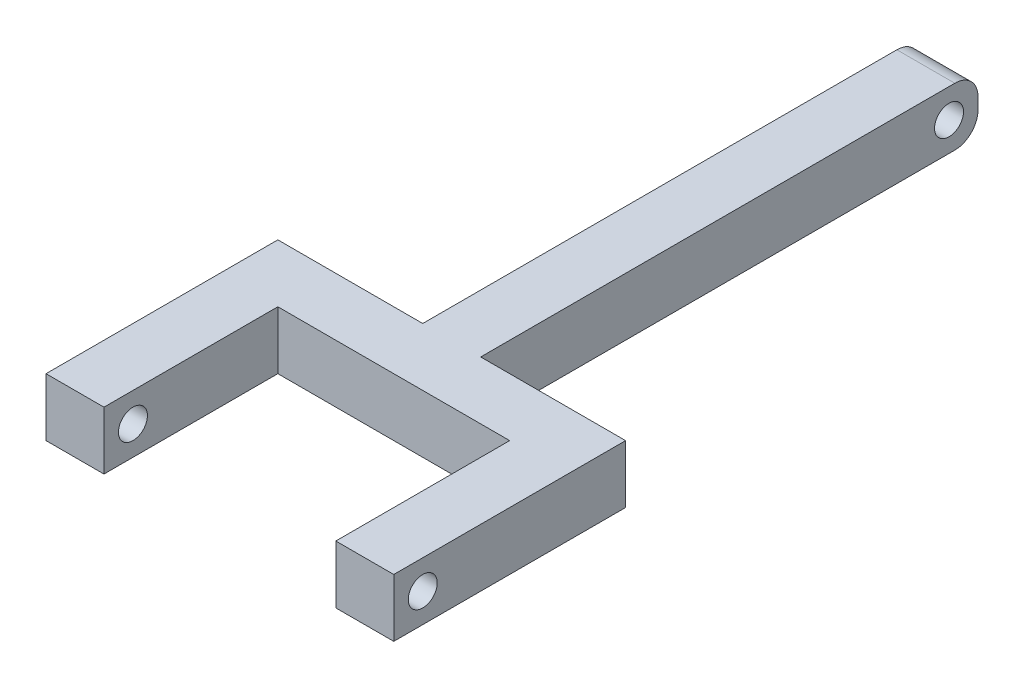
SolidWorks part; units mm, degrees
ref_plane "Front Plane" through (0, 0, 0) normal (0, 0, 1) x (1, 0, 0)
ref_plane "Top Plane" through (0, 0, 0) normal (0, 1, 0) x (1, 0, 0)
ref_plane "Right Plane" through (0, 0, 0) normal (1, 0, 0) x (0, 0, -1)
sketch "Sketch1" plane through (0, 0, 0) normal (0, 0, 1) x (1, 0, 0)
  line L1 (-6.35, -6.35) -> (6.35, -6.35)
  line L2 (-6.35, -6.35) -> (-6.35, 6.35)
  line L3 (-6.35, 6.35) -> (6.35, 6.35)
  line L4 (6.35, -6.35) -> (6.35, 6.35)
  point P4 (0, 6.35)
  point P6 (-6.35, 0)
  dimension "D1" = 12.7
  dimension "D2" = 12.7
  dimension "D3" = 0
  dimension "D4" = 0
extrude "Boss-Extrude1" add sketch "Sketch1" against normal blind 80.01 and the other way blind 41.656
sketch "Sketch4" plane through (0, 0, 0) normal (1, 0, 0) x (0, 0, -1)
  line L0 (-41.656, 6.35) -> (-41.656, -6.35)
  line L1 (-41.656, -6.35) -> (-28.956, -6.35)
  line L2 (-28.956, -6.35) -> (-28.956, 6.35)
  line L3 (-28.956, 6.35) -> (-41.656, 6.35)
  dimension "D1" = 12.7
extrude "Boss-Extrude2" add sketch "Sketch4" along normal mid plane 76.2
sketch "Sketch5" plane through (0, 0, 28.956) normal (0, 0, -1) x (-1, 0, 0)
  line L0 (-38.1, 6.35) -> (-6.35, 6.35) construction
  line L1 (-38.1, -6.35) -> (-25.4, -6.35)
  line L2 (-38.1, -6.35) -> (-38.1, 6.35)
  line L3 (-38.1, 6.35) -> (-25.4, 6.35)
  line L4 (-25.4, -6.35) -> (-25.4, 6.35)
  dimension "D1" = 12.7
extrude "Boss-Extrude3" add sketch "Sketch5" against normal blind 50.8
sketch "Sketch6" plane through (25.4, 0, 0) normal (-1, 0, 0) x (0, 0, 1)
  line L1 (79.756, -6.35) -> (79.756, 6.35) construction
  circle A0 centre (73.406, 0) radius 3.175
  dimension "D1" = 6.35
  dimension "D2" = 6.35
extrude "Cut-Extrude1" cut sketch "Sketch6" against normal blind 16.51
mirror "Mirror1" about plane through (0, 0, 0) normal (1, 0, 0) of "Cut-Extrude1", "Boss-Extrude3"
sketch "Sketch7" plane through (-6.35, 0, 0) normal (-1, 0, 0) x (0, 0, 1)
  line L1 (-80.01, 6.35) -> (-80.01, -6.35) construction
  line L2 (28.956, 6.35) -> (-80.01, 6.35) construction
  circle A0 centre (-73.66, 0) radius 3.175
  point P2 (-80.01, 0)
  dimension "D1" = 6.35
  dimension "D2" = 6.35
extrude "Cut-Extrude2" cut sketch "Sketch7" against normal through all
fillet "Fillet1" radius 5.08 2 edges at (0, -6.35, -80.01) (0, 6.35, -80.01)
